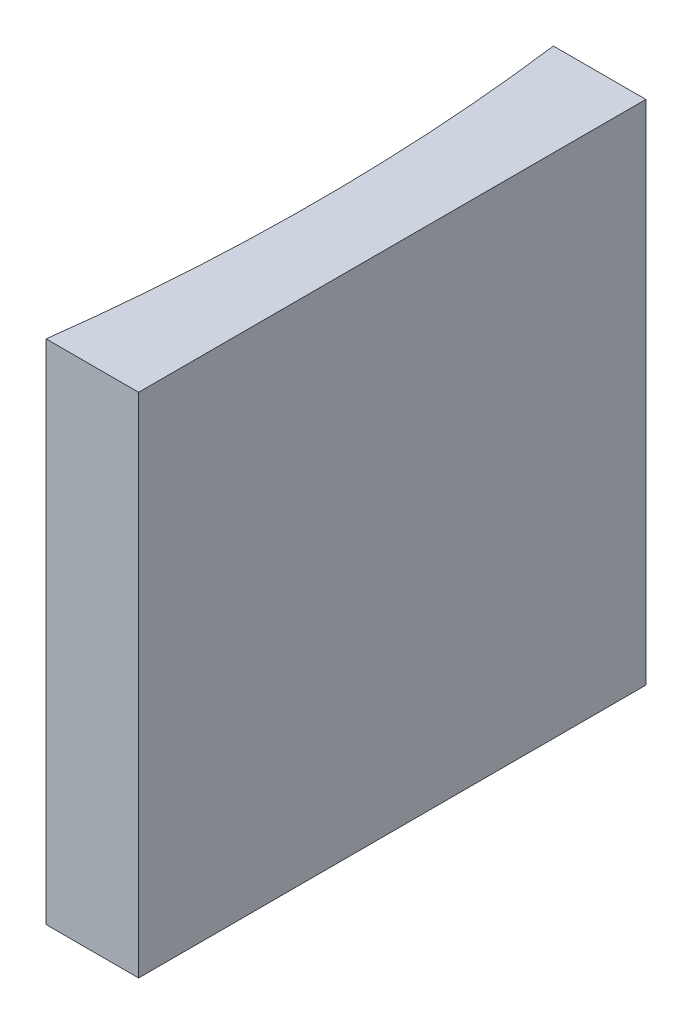
SolidWorks part; units mm, degrees
ref_plane "前视基准面" through (0, 0, 0) normal (0, 0, 1) x (1, 0, 0)
ref_plane "上视基准面" through (0, 0, 0) normal (0, 1, 0) x (1, 0, 0)
ref_plane "右视基准面" through (0, 0, 0) normal (1, 0, 0) x (0, 0, -1)
sketch "草图1" plane through (0, 0, 0) normal (0, 1, 0) x (1, 0, 0)
  line L0 (0, 0) -> (0, -20)
  line L1 (0, 0) -> (-3.6474, 0)
  line L2 (0, -20) -> (-3.6474, -20)
  line L3 (8.2336, -10) -> (-10.4405, -10) construction
  arc A0 (-3.6474, -20) -> (-3.6474, 0) centre (-80.55, -10) ccw
  point P7 (-3, -10)
  point P8 (0, -10)
  dimension "D2" = 77.55
  dimension "D3" = 3
  dimension "D1" = 20
extrude "凸台-拉伸1" add sketch "草图1" along normal blind 20
